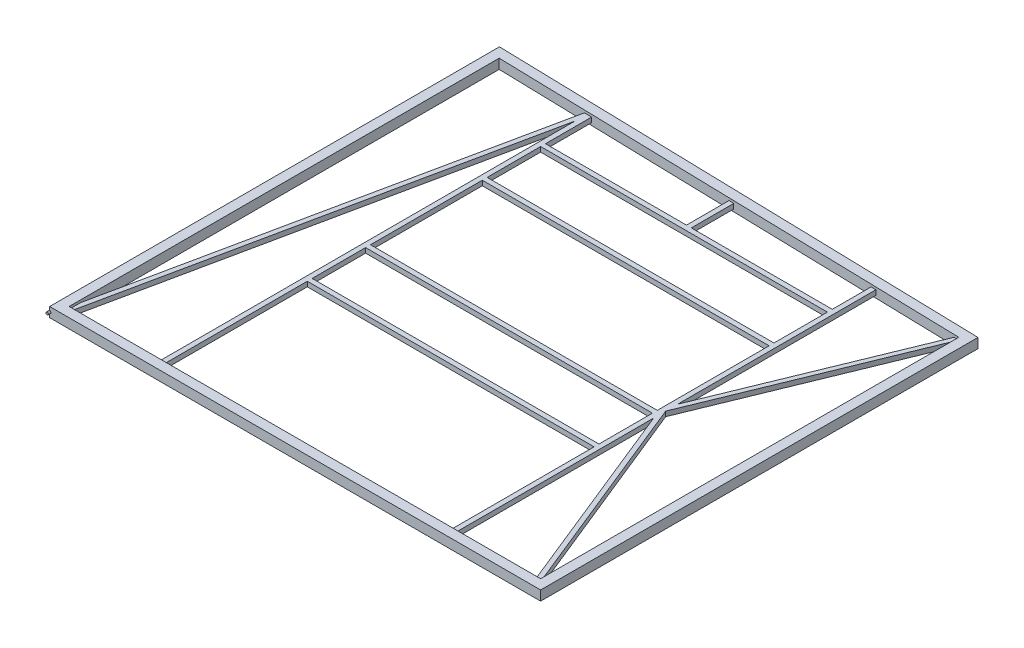
SolidWorks part; units mm, degrees
material "6063-T6"
ref_plane "Front Plane" through (0, 0, 0) normal (0, 0, 1) x (1, 0, 0)
ref_plane "Top Plane" through (0, 0, 0) normal (0, 1, 0) x (1, 0, 0)
ref_plane "Right Plane" through (0, 0, 0) normal (1, 0, 0) x (0, 0, -1)
sketch "Sketch1" plane through (0, 0, 0) normal (0, 1, 0) x (1, 0, 0)
  line L0 (0, 2298.7) -> (0, 0)
  line L1 (0, 0) -> (2514.6, 0)
  line L2 (2514.6, 0) -> (2514.6, 2235.2)
  line L3 (2514.6, 2235.2) -> (0, 2298.7)
  dimension "D1" = 2235.2
  dimension "D2" = 2514.6
  dimension "D3" = 2298.7
ref_plane "Plane1" through (0, 0, -1016) normal (0, 0, 1) x (1, 0, 0)
sketch "Sketch2" plane through (0, 0, -1016) normal (0, 0, 1) x (1, 0, 0)
  line L0 (-22.225, 22.225) -> (-22.225, -22.225)
  line L1 (-25.4, 25.4) -> (25.4, 25.4)
  line L2 (-25.4, 25.4) -> (-25.4, -25.4)
  line L3 (-25.4, -25.4) -> (25.4, -25.4)
  line L4 (25.4, 25.4) -> (25.4, -25.4)
  line L5 (-25.4, 25.4) -> (25.4, -25.4) construction
  line L6 (-25.4, -25.4) -> (25.4, 25.4) construction
  line L7 (-22.225, -22.225) -> (22.225, -22.225)
  line L8 (22.225, 22.225) -> (22.225, -22.225)
  line L9 (-22.225, 22.225) -> (22.225, 22.225)
  point P0 (0, 0)
  dimension "D1" = 50.8
  dimension "D2" = 50.8
  dimension "D3" = 3.175
sweep "Sweep1" add profiles "Sketch2" path "Sketch1"
sketch "Sketch4" plane through (0, 0, -25.4) normal (0, 0, -1) x (-1, 0, 0)
  line L1 (-2019.3, -12.7) -> (-2044.7, -12.7)
  line L2 (-2019.3, -12.7) -> (-2019.3, 12.7)
  line L3 (-2019.3, 12.7) -> (-2044.7, 12.7)
  line L4 (-2044.7, -12.7) -> (-2044.7, 12.7)
  line L5 (-2019.3, -12.7) -> (-2044.7, 12.7) construction
  line L6 (-2019.3, 12.7) -> (-2044.7, -12.7) construction
  line L7 (-2022.475, -9.525) -> (-2022.475, 9.525)
  line L8 (-2022.475, 9.525) -> (-2041.525, 9.525)
  line L9 (-2041.525, -9.525) -> (-2041.525, 9.525)
  line L10 (-2022.475, -9.525) -> (-2041.525, -9.525)
  line L11 (-2489.2, 25.4) -> (-2489.2, -25.4) construction
  line L12 (-495.3, -12.7) -> (-495.3, 12.7)
  line L13 (-495.3, -12.7) -> (-520.7, -12.7)
  line L14 (-520.7, -12.7) -> (-520.7, 12.7)
  line L15 (-495.3, 12.7) -> (-520.7, 12.7)
  line L16 (-498.475, -9.525) -> (-498.475, 9.525)
  line L17 (-498.475, 9.525) -> (-517.525, 9.525)
  line L18 (-517.525, -9.525) -> (-517.525, 9.525)
  line L19 (-498.475, -9.525) -> (-517.525, -9.525)
  line L20 (-25.4, 25.4) -> (-25.4, -25.4) construction
  point P0 (-2032, 0)
  point P5 (-508, 12.7)
  point P13 (-2489.2, 0)
  dimension "D1" = 457.2
  dimension "D2" = 25.4
  dimension "D3" = 25.4
  dimension "D6" = 482.6
  dimension "D4" = 3.175
  dimension "D5" = 2
extrude "Boss-Extrude2" add sketch "Sketch4" along normal up to surface (2196.2581 mm away)
sketch "Sketch5" plane through (520.7, 0, 0) normal (1, 0, 0) x (0, 0, -1)
  line L0 (2260.1429, -12.7) -> (25.4, -12.7) construction
  line L1 (800.1, 12.7) -> (774.7, 12.7)
  line L2 (800.1, 12.7) -> (800.1, -12.7)
  line L3 (800.1, -12.7) -> (774.7, -12.7)
  line L4 (774.7, 12.7) -> (774.7, -12.7)
  line L5 (800.1, 12.7) -> (774.7, -12.7) construction
  line L6 (800.1, -12.7) -> (774.7, 12.7) construction
  line L7 (2260.1429, 12.7) -> (25.4, 12.7) construction
  line L8 (25.4, 12.7) -> (25.4, -12.7) construction
  line L9 (1104.9, 12.7) -> (1079.5, 12.7)
  line L10 (1104.9, 12.7) -> (1104.9, -12.7)
  line L11 (1104.9, -12.7) -> (1079.5, -12.7)
  line L12 (1079.5, 12.7) -> (1079.5, -12.7)
  line L13 (1104.9, 12.7) -> (1079.5, -12.7) construction
  line L14 (1104.9, -12.7) -> (1079.5, 12.7) construction
  line L15 (796.925, 9.525) -> (796.925, -9.525)
  line L16 (796.925, -9.525) -> (777.875, -9.525)
  line L17 (777.875, 9.525) -> (777.875, -9.525)
  line L18 (796.925, 9.525) -> (777.875, 9.525)
  line L19 (1101.725, 9.525) -> (1082.675, 9.525)
  line L20 (1082.675, 9.525) -> (1082.675, -9.525)
  line L21 (1101.725, -9.525) -> (1082.675, -9.525)
  line L22 (1101.725, 9.525) -> (1101.725, -9.525)
  line L23 (1714.5, 12.7) -> (1714.5, -12.7)
  line L24 (1714.5, 12.7) -> (1689.1, 12.7)
  line L25 (1689.1, 12.7) -> (1689.1, -12.7)
  line L26 (1714.5, -12.7) -> (1689.1, -12.7)
  line L27 (1711.325, 9.525) -> (1711.325, -9.525)
  line L28 (1711.325, -9.525) -> (1692.275, -9.525)
  line L29 (1692.275, 9.525) -> (1692.275, -9.525)
  line L30 (1711.325, 9.525) -> (1692.275, 9.525)
  line L31 (2019.3, 12.7) -> (1993.9, 12.7)
  line L32 (1993.9, 12.7) -> (1993.9, -12.7)
  line L33 (2019.3, -12.7) -> (1993.9, -12.7)
  line L34 (2019.3, 12.7) -> (2019.3, -12.7)
  line L35 (2016.125, 9.525) -> (1997.075, 9.525)
  line L36 (1997.075, 9.525) -> (1997.075, -9.525)
  line L37 (2016.125, -9.525) -> (1997.075, -9.525)
  line L38 (2016.125, 9.525) -> (2016.125, -9.525)
  point P0 (787.4, 0)
  point P11 (1092.2, 0)
  point P26 (1701.8, 12.7)
  dimension "D1" = 25.4
  dimension "D2" = 762
  dimension "D3" = 25.4
  dimension "D4" = 304.8
  dimension "D8" = 609.6
  dimension "D5" = 3.175
  dimension "D6" = 3.175
  dimension "D7" = 2
extrude "Boss-Extrude3" add sketch "Sketch5" along normal up to surface (1498.6 mm away) up to face at (2019.3, 0, -1123.8497)
sketch "Sketch6" plane through (0, 0, -25.4) normal (0, 0, -1) x (-1, 0, 0)
  line L1 (-12.7, -12.7) -> (-38.1, -12.7)
  line L2 (-12.7, -12.7) -> (-12.7, 12.7)
  line L3 (-12.7, 12.7) -> (-38.1, 12.7)
  line L4 (-38.1, -12.7) -> (-38.1, 12.7)
  line L5 (-12.7, -12.7) -> (-38.1, 12.7) construction
  line L6 (-12.7, 12.7) -> (-38.1, -12.7) construction
  line L7 (-25.4, 25.4) -> (-25.4, -25.4) construction
  point P0 (-25.4, 0)
  point P8 (-25.4, 0)
  dimension "D1" = 25.4
  dimension "D2" = 25.4
sketch "Sketch7" plane through (0, 25.4, 0) normal (0, 1, 0) x (1, 0, 0)
  line L0 (25.4, 25.4) -> (495.3, 2260.7843)
sweep "Sweep2" add profiles "Sketch6" path "Sketch7"
sketch "Sketch8" plane through (0, 0, -2019.3) normal (0, 0, -1) x (-1, 0, 0)
  line L0 (-2019.3, 12.7) -> (-520.7, 12.7) construction
  line L1 (-1257.3, -12.7) -> (-1282.7, -12.7)
  line L2 (-1257.3, -12.7) -> (-1257.3, 12.7)
  line L3 (-1257.3, 12.7) -> (-1282.7, 12.7)
  line L4 (-1282.7, -12.7) -> (-1282.7, 12.7)
  line L5 (-1257.3, -12.7) -> (-1282.7, 12.7) construction
  line L6 (-1257.3, 12.7) -> (-1282.7, -12.7) construction
  line L7 (-2019.3, -12.7) -> (-520.7, -12.7) construction
  line L8 (-1260.475, -9.525) -> (-1260.475, 9.525)
  line L9 (-1260.475, 9.525) -> (-1279.525, 9.525)
  line L10 (-1279.525, -9.525) -> (-1279.525, 9.525)
  line L11 (-1260.475, -9.525) -> (-1279.525, -9.525)
  point P0 (-1270, 0)
  point P9 (-1270, -12.7)
  dimension "D1" = 25.4
  dimension "D2" = 3.175
extrude "Boss-Extrude4" add sketch "Sketch8" along normal up to surface (221.6005 mm away)
sketch "Sketch9" plane through (0, 0, -25.4) normal (0, 0, -1) x (-1, 0, 0)
  line L0 (-2489.2, 25.4) -> (-2489.2, -25.4) construction
  line L1 (-2463.8, -12.7) -> (-2489.2, -12.7)
  line L2 (-2463.8, -12.7) -> (-2463.8, 12.7)
  line L3 (-2463.8, 12.7) -> (-2489.2, 12.7)
  line L4 (-2489.2, -12.7) -> (-2489.2, 12.7)
  line L5 (-2463.8, -12.7) -> (-2489.2, 12.7) construction
  line L6 (-2463.8, 12.7) -> (-2489.2, -12.7) construction
  line L7 (-2466.975, -9.525) -> (-2466.975, 9.525)
  line L8 (-2466.975, 9.525) -> (-2486.025, 9.525)
  line L9 (-2486.025, -9.525) -> (-2486.025, 9.525)
  line L10 (-2466.975, -9.525) -> (-2486.025, -9.525)
  point P0 (-2476.5, 0)
  point P7 (-2489.2, 0)
  dimension "D1" = 25.4
  dimension "D2" = 25.4
  dimension "D3" = 3.175
sketch "Sketch10" plane through (0, 25.4, 0) normal (0, 1, 0) x (1, 0, 0)
  line L0 (2489.2, 25.4) -> (2044.7, 1123.529)
  line L1 (2044.7, 2221.6581) -> (2044.7, 25.4) construction
  line L2 (2044.7, 1123.529) -> (2489.2, 2210.4333)
sweep "Sweep4" add profiles "Sketch9" path "Sketch10"
sketch "Sketch11" plane through (0, 0, 25.4) normal (0, 0, 1) x (1, 0, 0)
  line L0 (-25.4, -25.4) -> (-25.4, 25.4) construction
  circle A0 centre (-25.4, 0) radius 6.35
  point P7 (-25.4, 0)
  dimension "D1" = 12.7
extrude "Boss-Extrude5" add sketch "Sketch11" along normal mid plane 25.4
ref_plane "NORMAL PIN PLANE" through (0, 0, -2324.7495) normal (0, 0, 1) x (1, 0, 0)
sketch "Sketch13" plane through (0, 0, -2324.7495) normal (0, 0, 1) x (1, 0, 0)
  line L0 (-25.4, -25.4) -> (-25.4, 25.4) construction
  circle A0 centre (-25.4, 0) radius 6.35
  point P7 (-25.4, 0)
  dimension "D1" = 12.7
extrude "Boss-Extrude6" add sketch "Sketch13" along normal mid plane 31.75
